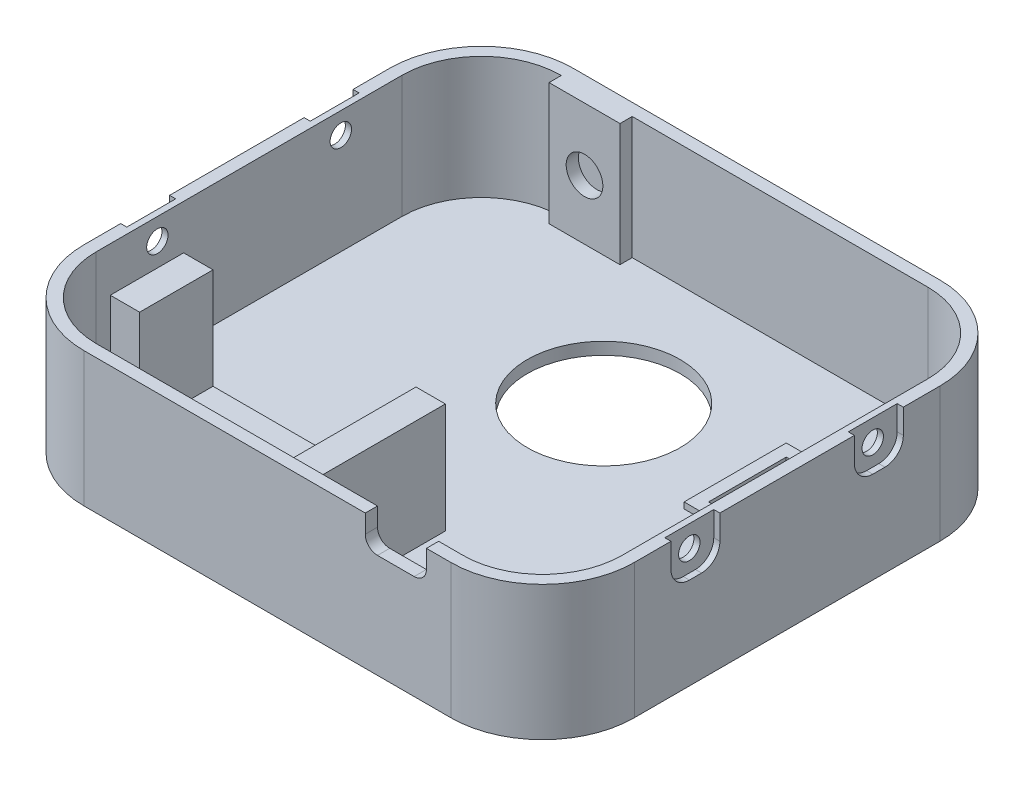
SolidWorks part; units mm, degrees
ref_plane "Front Plane" through (0, 0, 0) normal (0, 0, 1) x (1, 0, 0)
ref_plane "Top Plane" through (0, 0, 0) normal (0, 1, 0) x (1, 0, 0)
ref_plane "Right Plane" through (0, 0, 0) normal (1, 0, 0) x (0, 0, -1)
sketch "Sketch1" plane through (0, 0, 0) normal (0, 1, 0) x (1, 0, 0)
  line L1 (-30, 25) -> (30, 25)
  line L2 (-45, 10) -> (-45, -40)
  line L3 (-30, -55) -> (30, -55)
  line L4 (45, 10) -> (45, -40)
  arc A1 (30, 25) -> (45, 10) centre (30, 10) cw
  arc A2 (45, -40) -> (30, -55) centre (30, -40) cw
  arc A3 (-30, -55) -> (-45, -40) centre (-30, -40) cw
  arc A4 (-45, 10) -> (-30, 25) centre (-30, 10) cw
  point P10 (45, 25)
  point P15 (-45, -55)
  point P18 (-45, 25)
  dimension "D1" = 25
  dimension "D5" = 15
  dimension "D2" = 80
  dimension "D3" = 90
  dimension "D4" = 45
extrude "Boss-Extrude1" add sketch "Sketch1" along normal blind 2
sketch "Sketch4" plane through (0, 2, 0) normal (0, 1, 0) x (1, 0, 0)
  line L0 (30, 23) -> (-30, 23)
  line L1 (-43, 10) -> (-43, -40)
  line L2 (-30, -53) -> (30, -53)
  line L3 (43, -40) -> (43, 10)
  line L4 (30, 25) -> (-30, 25)
  line L5 (-45, 10) -> (-45, -40)
  line L6 (-30, -55) -> (30, -55)
  line L7 (45, -40) -> (45, 10)
  line L8 (30, 25) -> (-30, 25)
  line L9 (-45, 10) -> (-45, -40)
  line L10 (-30, -55) -> (30, -55)
  line L11 (45, -40) -> (45, 10)
  arc A0 (-30, 23) -> (-43, 10) centre (-30, 10) ccw
  arc A1 (-43, -40) -> (-30, -53) centre (-30, -40) ccw
  arc A2 (30, -53) -> (43, -40) centre (30, -40) ccw
  arc A3 (43, 10) -> (30, 23) centre (30, 10) ccw
  arc A4 (45, 10) -> (30, 25) centre (30, 10) ccw
  arc A5 (-30, 25) -> (-45, 10) centre (-30, 10) ccw
  arc A6 (-45, -40) -> (-30, -55) centre (-30, -40) ccw
  arc A7 (30, -55) -> (45, -40) centre (30, -40) ccw
  arc A8 (45, 10) -> (30, 25) centre (30, 10) ccw
  arc A9 (-30, 25) -> (-45, 10) centre (-30, 10) ccw
  arc A10 (-45, -40) -> (-30, -55) centre (-30, -40) ccw
  arc A11 (30, -55) -> (45, -40) centre (30, -40) ccw
  dimension "D1" = 0
  dimension "D2" = 2
extrude "Boss-Extrude2" add sketch "Sketch4" along normal blind 20
sketch "Sketch3" plane through (0, 0, 0) normal (0, -1, 0) x (1, 0, 0)
  circle A0 centre (0, 0) radius 12.5
  dimension "D1" = 25
extrude "Cut-Extrude2" cut sketch "Sketch3" against normal through all
sketch "Sketch5" plane through (0, 2, 0) normal (0, 1, 0) x (1, 0, 0)
  line L1 (-36.0029, -53) -> (5.1, -53)
  line L2 (-37.7, -51.3029) -> (-37.7, -31)
  line L3 (-37.7, -31) -> (5.1, -31)
  line L4 (5.1, -53) -> (5.1, -31)
  line L7 (-43, 10) -> (-43, -40) construction
  line L9 (-30, -53) -> (30, -53) construction
  line L10 (-37.7, -51.3029) -> (-36.0029, -53)
  dimension "D1" = 22
  dimension "D2" = 42.8
  dimension "D3" = 135
  dimension "D4" = 5.3
  dimension "D5" = 2.4
extrude "Boss-Extrude3" add sketch "Sketch5" along normal blind 1.5
sketch "Sketch6" plane through (0, 2, 0) normal (0, 1, 0) x (1, 0, 0)
  line L0 (21.5, 8.35) -> (38.9, 8.35)
  line L1 (23.5, 6.35) -> (36.9, 6.35)
  line L2 (23.5, 6.35) -> (23.5, -6.35)
  line L3 (23.5, -6.35) -> (36.9, -6.35)
  line L4 (36.9, 6.35) -> (36.9, -6.35)
  line L5 (23.5, 6.35) -> (36.9, -6.35) construction
  line L6 (23.5, -6.35) -> (36.9, 6.35) construction
  line L7 (38.9, 8.35) -> (38.9, -8.35)
  line L8 (21.5, -8.35) -> (38.9, -8.35)
  line L9 (21.5, 8.35) -> (21.5, -8.35)
  point P0 (30.2, 0)
  dimension "D1" = 30.2
  dimension "D2" = 13.4
  dimension "D3" = 12.7
  dimension "D4" = 2
extrude "Boss-Extrude4" add sketch "Sketch6" along normal blind 1
sketch "Sketch7" plane through (0, 0, -23) normal (0, 0, 1) x (1, 0, 0)
  line L1 (-29.94, 2) -> (-18.34, 2)
  line L2 (-29.94, 2) -> (-29.94, 22)
  line L3 (-29.94, 22) -> (-18.34, 22)
  line L4 (-18.34, 2) -> (-18.34, 22)
  line L7 (-30, 22) -> (-30, 2) construction
  line L8 (30, 22) -> (-30, 22) construction
  line L9 (30, 2) -> (-30, 2) construction
  circle A0 centre (-24.14, 11.75) radius 3
  point P11 (-24.14, 2)
  dimension "D1" = 6
  dimension "D2" = 11.6
  dimension "D3" = 9.75
  dimension "D4" = 5.86
extrude "Boss-Extrude5" add sketch "Sketch7" along normal blind 2
sketch "Sketch8" plane through (0, 3.5, 0) normal (0, 1, 0) x (1, 0, 0)
  line L1 (-37.7, -31) -> (-32.9, -31)
  line L2 (-37.7, -31) -> (-37.7, -43)
  line L4 (-32.9, -31) -> (-32.9, -43)
  line L5 (5.1, -31) -> (-37.7, -31) construction
  line L6 (5.1, -51) -> (0.3, -51)
  line L7 (5.1, -51) -> (5.1, -31)
  line L8 (5.1, -31) -> (0.3, -31)
  line L9 (0.3, -51) -> (0.3, -31)
  line L10 (5.1, -53) -> (5.1, -31) construction
  line L11 (-30, -53) -> (5.1, -53) construction
  line L13 (-32.9, -43) -> (-37.7, -43)
  dimension "D1" = 4.8
  dimension "D2" = 4.8
  dimension "D3" = 2
  dimension "D4" = 10
extrude "Boss-Extrude6" add sketch "Sketch8" along normal blind 16.5
sketch "Sketch9" plane through (0, 0, 31) normal (0, 0, -1) x (-1, 0, 0)
  line L0 (-5.1, 20) -> (-0.3, 20) construction
  line L1 (-2.7, 20) -> (-2.7, 7.75) construction
  line L2 (35.3, 20) -> (35.3, 7.75) construction
  line L3 (32.9, 20) -> (37.7, 20) construction
  circle A0 centre (-2.7, 15.75) radius 0.5
  circle A1 centre (-2.7, 7.75) radius 0.5
  circle A2 centre (35.3, 15.75) radius 0.5
  circle A3 centre (35.3, 7.75) radius 0.5
  dimension "D1" = 4.25
  dimension "D5" = 1
  dimension "D2" = 8
  dimension "D3" = 8
  dimension "D4" = 4.25
extrude "Cut-Extrude3" cut sketch "Sketch9" against normal blind 5
sketch "Sketch10" plane through (0, 0, 55) normal (0, 0, 1) x (1, 0, 0)
  line L0 (30, 22) -> (30, 0) construction
  line L1 (16, 22) -> (26, 22)
  line L2 (16, 22) -> (16, 19)
  line L3 (18, 17) -> (24, 17)
  line L4 (26, 22) -> (26, 19)
  line L5 (16, 22) -> (26, 17) construction
  line L6 (16, 17) -> (26, 22) construction
  line L7 (-30, 22) -> (30, 22) construction
  arc A0 (24, 17) -> (26, 19) centre (24, 19) ccw
  arc A1 (16, 19) -> (18, 17) centre (18, 19) ccw
  point P0 (21, 19.5)
  dimension "D4" = 2
  dimension "D1" = 10
  dimension "D2" = 5
  dimension "D3" = 9
extrude "Cut-Extrude4" cut sketch "Sketch10" against normal up to surface (2 mm away) up to face at (1.7, 9.1667, 53)
sketch "Sketch11" plane through (-43, 0, 0) normal (1, 0, 0) x (0, 0, -1)
  line L0 (10, 22) -> (-40, 22) construction
  line L1 (-30, 18.5) -> (0, 18.5) construction
  circle A0 centre (-30, 18.5) radius 1.75
  circle A1 centre (0, 18.5) radius 1.75
  point P4 (-15, 22)
  point P7 (-15, 18.5)
  dimension "D1" = 30
  dimension "D3" = 3.5
  dimension "D2" = 3.5
extrude "Cut-Extrude5" cut sketch "Sketch11" against normal up to next (2 mm away)
sketch "Sketch12" plane through (-45, 0, 0) normal (-1, 0, 0) x (0, 0, 1)
  line L0 (-10, 22) -> (40, 22) construction
  line L5 (-4, 22) -> (4, 22)
  line L6 (-4, 22) -> (-4, 18)
  line L7 (26, 22) -> (34, 22)
  line L8 (26, 22) -> (26, 18)
  line L9 (29, 15) -> (31, 15)
  line L10 (34, 22) -> (34, 18)
  line L11 (26, 22) -> (34, 15) construction
  line L12 (26, 15) -> (34, 22) construction
  line L13 (-1, 15) -> (1, 15)
  line L14 (4, 22) -> (4, 18)
  line L15 (-4, 22) -> (4, 15) construction
  line L16 (-4, 15) -> (4, 22) construction
  circle A0 centre (0, 18.5) radius 1.75 construction
  arc A1 (31, 15) -> (34, 18) centre (31, 18) ccw
  arc A2 (29, 15) -> (26, 18) centre (29, 18) cw
  arc A3 (4, 18) -> (1, 15) centre (1, 18) cw
  arc A4 (-1, 15) -> (-4, 18) centre (-1, 18) cw
  point P0 (0, 18.5)
  point P5 (30, 18.5)
  dimension "D3" = 3
  dimension "D1" = 8
  dimension "D2" = 8
extrude "Cut-Extrude6" cut sketch "Sketch12" against normal blind 1
mirror "Mirror1" about plane through (0, 0, 0) normal (1, 0, 0) of "Cut-Extrude6", "Cut-Extrude5"
